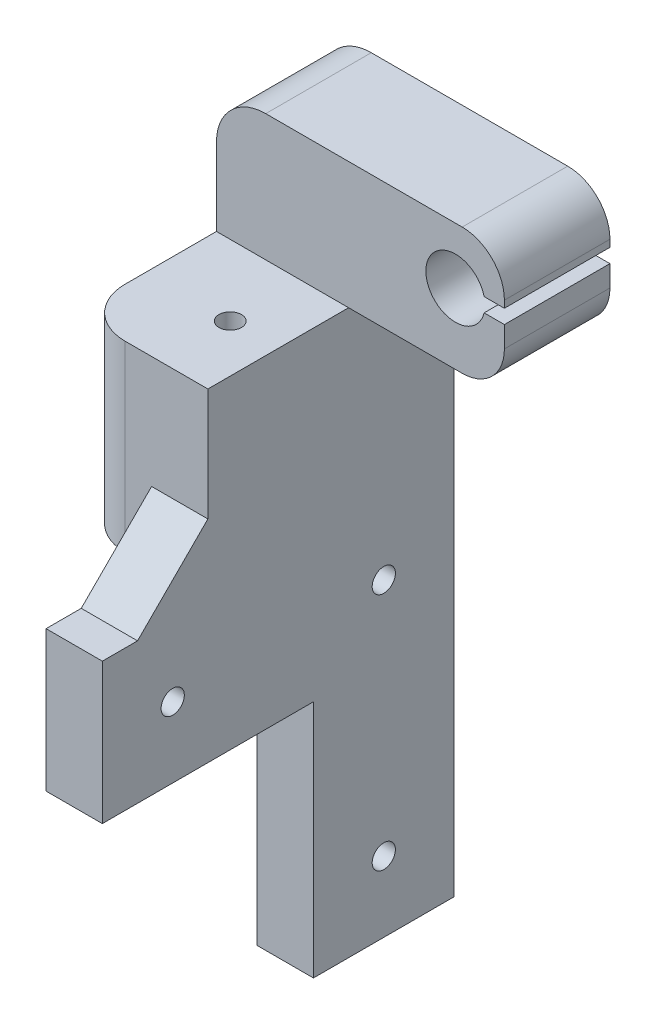
SolidWorks part; units mm, degrees
material "ABS"
ref_plane "前视基准面" through (0, 0, 0) normal (0, 0, 1) x (1, 0, 0)
ref_plane "上视基准面" through (0, 0, 0) normal (0, 1, 0) x (1, 0, 0)
ref_plane "右视基准面" through (0, 0, 0) normal (1, 0, 0) x (0, 0, -1)
sketch "草图1" plane through (0, 0, 0) normal (0, 0, 1) x (1, 0, 0)
  line L0 (0, 0) -> (8, 0)
  line L1 (0, 0) -> (0, 54)
  line L2 (8, 0) -> (8, 80)
  line L3 (0, 54) -> (-10.78, 54)
  line L4 (-10.78, 54) -> (-10.78, 98)
  line L5 (-10.78, 98) -> (30.14, 98)
  line L6 (8, 80) -> (30.14, 80)
  line L7 (30.14, 80) -> (30.14, 98)
extrude "凸台-拉伸1" add sketch "草图1" along normal blind 15
sketch "草图2" plane through (0, 0, 15) normal (0, 0, 1) x (1, 0, 0)
  line L1 (8, 80) -> (-10.78, 80)
  line L2 (8, 80) -> (8, 54)
  line L3 (8, 54) -> (-10.78, 54)
  line L4 (-10.78, 80) -> (-10.78, 54)
extrude "凸台-拉伸2" add sketch "草图2" along normal blind 20
sketch "草图3" plane through (0, 0, 15) normal (0, 0, 1) x (1, 0, 0)
  line L1 (0, 54) -> (8, 54)
  line L2 (0, 54) -> (0, 0)
  line L3 (0, 0) -> (8, 0)
  line L4 (8, 54) -> (8, 0)
extrude "凸台-拉伸3" add sketch "草图3" along normal blind 5
sketch "草图4" plane through (0, 0, 20) normal (0, 0, 1) x (1, 0, 0)
  line L0 (8, 0) -> (8, 54) construction
  line L1 (0, 54) -> (8, 54)
  line L2 (0, 54) -> (0, 34)
  line L3 (0, 34) -> (8, 34)
  line L4 (8, 54) -> (8, 34)
extrude "凸台-拉伸4" add sketch "草图4" along normal blind 30
sketch "草图5" plane through (0, 0, 15) normal (0, 0, 1) x (1, 0, 0)
  line L2 (30.14, 80) -> (30.14, 98) construction
  line L3 (30.14, 90) -> (30.14, 91)
  line L4 (30.14, 91) -> (27.2592, 91)
  line L6 (27.2592, 89) -> (30.14, 89)
  line L7 (30.14, 89) -> (30.14, 90)
  arc A0 (27.2592, 91) -> (27.2592, 89) centre (23.18, 90) ccw
extrude "切除-拉伸2" cut sketch "草图5" against normal blind 30
fillet "圆角1" radius 6 1 edges at (30.14, 98, 7.5)
fillet "圆角2" radius 6 1 edges at (30.14, 80, 7.5)
fillet "圆角3" radius 7 1 edges at (-10.78, 98, 7.5)
fillet "圆角4" radius 7 1 edges at (-10.78, 67, 35)
chamfer "倒角1" distance 10 angle 45 1 edges at (4, 54, 35)
chamfer "倒角2" distance 4 angle 45 1 edges
sketch "草图6" plane through (0, 80, 0) normal (0, 1, 0) x (1, 0, 0)
  circle A1 centre (1.22, -25.05) radius 1.6
extrude "切除-拉伸3" cut sketch "草图6" against normal blind 179
sketch "草图9" plane through (0, 0, 0) normal (-1, 0, 0) x (0, 0, 1)
  line L0 (20, 34) -> (20, 54)
  line L1 (20, 54) -> (40.5372, 54)
  line L2 (40.5372, 54) -> (40.5372, 34)
  line L3 (50, 34) -> (26.0852, 34) construction
  line L4 (40.5372, 34) -> (20, 34)
extrude "切除-拉伸4" cut sketch "草图9" along normal blind 179
sketch "草图10" plane through (0, 0, 0) normal (-1, 0, 0) x (0, 0, 1)
  circle A0 centre (40, 44) radius 1.65
  circle A1 centre (10, 10) radius 1.65
  circle A2 centre (10, 44) radius 1.65
extrude "切除-拉伸5" cut sketch "草图10" against normal blind 179
